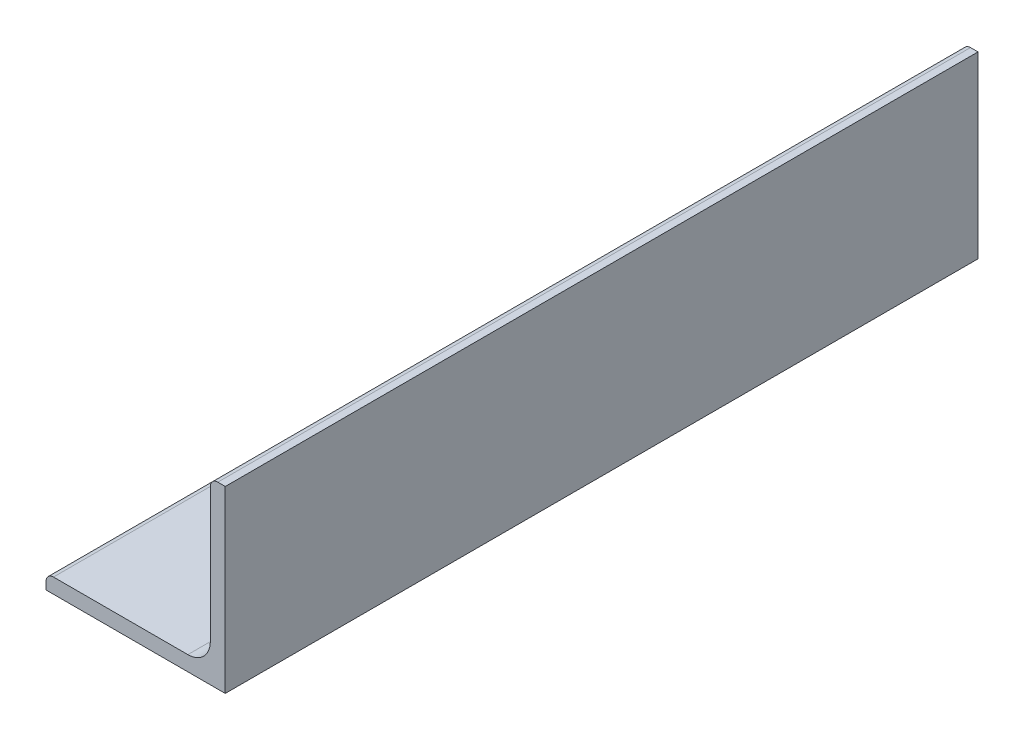
SolidWorks part; units mm, degrees
ref_plane "Front Plane" through (0, 0, 0) normal (0, 0, 1) x (1, 0, 0)
ref_plane "Top Plane" through (0, 0, 0) normal (0, 1, 0) x (1, 0, 0)
ref_plane "Right Plane" through (0, 0, 0) normal (1, 0, 0) x (0, 0, -1)
sketch "Sketch0" plane through (0, 0, 0) normal (0, 0, 1) x (1, 0, 0)
  line L0 (-19.05, -19.05) -> (19.05, -19.05)
  line L1 (19.05, -19.05) -> (19.05, 19.05)
  line L2 (19.05, 0) -> (0, 0) construction
  line L3 (0, 0) -> (0, -19.05) construction
  line L4 (15.875, -11.0998) -> (15.875, 19.05) construction
  line L5 (11.0998, -15.875) -> (-19.05, -15.875) construction
  arc A0 (15.875, -11.0998) -> (11.0998, -15.875) centre (11.0998, -11.0998) cw
  point P3 (14.4764, -14.4764)
  dimension "Inside Corner Radius" = 4.7752
  dimension "Outside Height" = 38.1
  dimension "Inside Height" = 34.925
  dimension "Inside Width" = 34.925
  dimension "Wall Thickness" = 3.175
  dimension "D1" = 3.175
  dimension "Outside Width" = 38.1
sketch "Sketch1" plane through (0, 0, 0) normal (1, 0, 0) x (0, 0, -1)
  line L0 (609.6, 0) -> (-609.6, 0)
  point P4 (0, 0)
  dimension "Length" = 1219.2
sketch "Sketch2" plane through (0, 0, 0) normal (0, 0, 1) x (1, 0, 0)
  line L0 (-19.05, -19.05) -> (19.05, -19.05)
  line L1 (19.05, -19.05) -> (19.05, 19.05)
  line L2 (19.05, 19.05) -> (15.875, 19.05) construction
  line L3 (15.875, 17.4625) -> (15.875, -11.0998)
  line L4 (11.0998, -15.875) -> (-17.4625, -15.875)
  line L5 (-19.05, -19.05) -> (-19.05, -15.875) construction
  line L6 (17.4625, 19.05) -> (19.05, 19.05)
  line L7 (-19.05, -17.4625) -> (-19.05, -19.05)
  line L8 (19.05, 0) -> (0, 0) construction
  line L9 (0, 0) -> (0, -19.05) construction
  arc A0 (15.875, 17.4625) -> (17.4625, 19.05) centre (17.4625, 17.4625) cw
  arc A1 (-19.05, -17.4625) -> (-17.4625, -15.875) centre (-17.4625, -17.4625) cw
  arc A2 (15.875, -11.0998) -> (11.0998, -15.875) centre (11.0998, -11.0998) cw
  dimension "Inside Radius" = 4.7752
  dimension "Height" = 38.1
  dimension "Width" = 38.1
  dimension "Thickness" = 3.175
extrude "Boss-Extrude1" add sketch "Sketch2" along normal mid plane 1219.2
sketch "Break Locations" plane through (0, 0, 0) normal (1, 0, 0) x (0, 0, -1)
  line L0 (-570.738, 0) -> (570.738, 0)
  line L1 (-609.6, -19.05) -> (-609.6, 19.05) construction
  line L2 (609.6, -19.05) -> (609.6, 19.05) construction
  point P0 (-577.215, 0)
  point P1 (577.215, 0)
  point P10 (0, 0)
  point P11 (570.738, 0)
  point P13 (-570.738, 0)
  dimension "D1" = 32.385
  dimension "D2" = 32.385
  dimension "D3" = 38.862
sketch "Sketch3" plane through (19.05, 0, 0) normal (1, 0, 0) x (0, 0, -1)
  line L5 (-609.6, -19.05) -> (609.6, -19.05) construction
  line L6 (609.6, 19.05) -> (-25.6, 19.05)
  line L7 (609.6, 19.05) -> (609.6, -19.05)
  line L8 (609.6, -19.05) -> (-25.6, -19.05)
  line L9 (-25.6, 19.05) -> (-25.6, -19.05)
  line L10 (-609.6, -19.05) -> (-609.6, 19.05) construction
  dimension "D1" = 584
extrude "Cut-Extrude1" cut sketch "Sketch3" against normal blind 60 contours L7 L6 L9 L8
sketch "Sketch4" plane through (19.05, 0, 0) normal (1, 0, 0) x (0, 0, -1)
  line L0 (-609.6, -19.05) -> (-25.6, -19.05) construction
  line L1 (-25.6, 19.05) -> (-449.6, 19.05)
  line L2 (-25.6, 19.05) -> (-25.6, -19.05)
  line L3 (-25.6, -19.05) -> (-449.6, -19.05)
  line L4 (-449.6, 19.05) -> (-449.6, -19.05)
  line L5 (-609.6, -19.05) -> (-609.6, 19.05) construction
  dimension "D1" = 160
extrude "Cut-Extrude2" cut sketch "Sketch4" against normal blind 60 contours L2 L1 L4 L3
sketch "Sketch5" plane through (0, -15.875, 0) normal (0, 1, 0) x (1, 0, 0)
  line L0 (11.0998, -449.6) -> (-17.4625, -449.6)
  line L1 (-3.1813, -449.6) -> (-3.1813, -609.6)
  line L2 (11.0998, -609.6) -> (-17.4625, -609.6) construction
  line L3 (-3.1813, -609.6) -> (-17.4625, -609.6)
sketch "Sketch6" plane through (15.875, 0, 0) normal (-1, 0, 0) x (0, 0, 1)
  line L0 (449.6, 3.1813) -> (609.6, 3.1813)
  line L1 (449.6, 17.4625) -> (449.6, -11.0998) construction
  line L2 (609.6, 17.4625) -> (609.6, -11.0998) construction
  line L3 (609.6, 3.1813) -> (609.6, 17.4625)
equation "\"D1@Break Locations\" = .85 * \"Height@Sketch2\""
equation "\"D2@Break Locations\"=\"D1@Break Locations\""
equation "\"Thickness@Sketch2\" = \"Wall Thickness@Sketch0\""
equation "\"Height@Sketch2\" = \"Outside Height@Sketch0\""
equation "\"Width@Sketch2\" = \"Outside Width@Sketch0\""
equation "\"Inside Radius@Sketch2\" = \"Inside Corner Radius@Sketch0\""
equation "\"Length@Boss-Extrude1\" = \"Length@Sketch1\""
equation "\"D3@Break Locations\"=\"D2@Break Locations\"*1.2"
equation "\"D1@Sketch0\"=\"Wall Thickness@Sketch0\""
